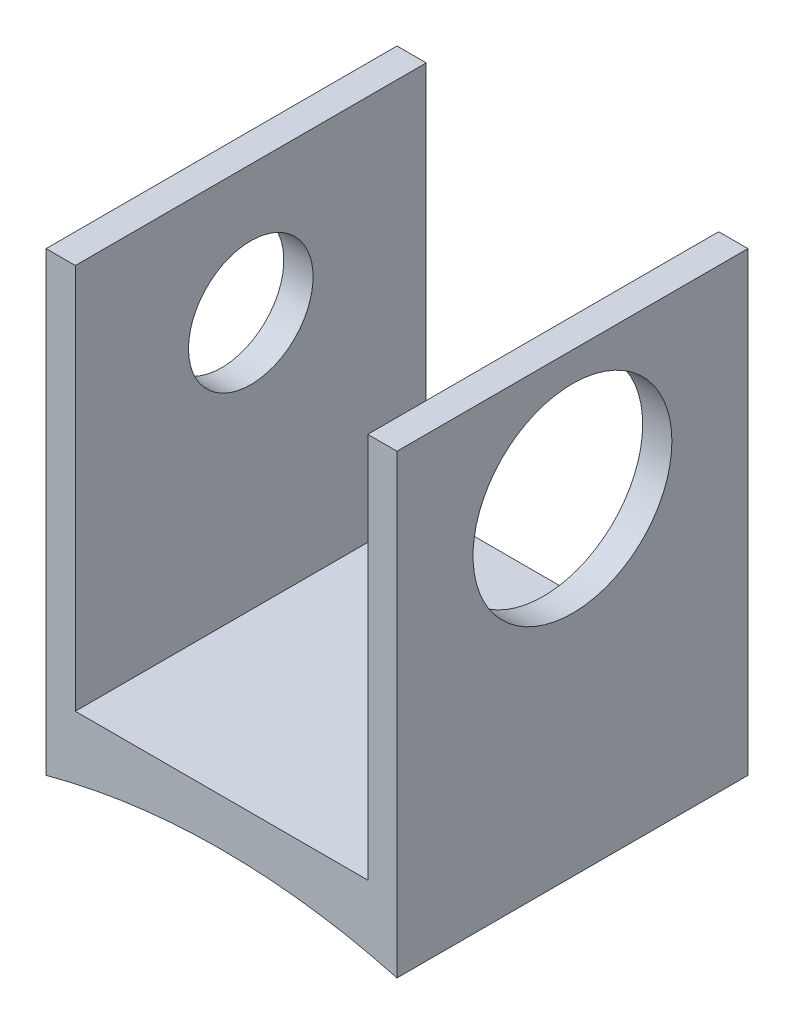
SolidWorks part; units mm, degrees
ref_plane "Front Plane" through (0, 0, 0) normal (0, 0, 1) x (1, 0, 0)
ref_plane "Top Plane" through (0, 0, 0) normal (0, 1, 0) x (1, 0, 0)
ref_plane "Right Plane" through (0, 0, 0) normal (1, 0, 0) x (0, 0, -1)
sketch "Sketch1" plane through (0, 0, 0) normal (0, 0, 1) x (1, 0, 0)
  line L0 (-3.3539, 7.6142) -> (-3.3539, -2.2918)
  line L1 (-3.3539, -2.2918) -> (4.2661, -2.2918)
  line L2 (4.2661, -2.2918) -> (4.2661, 7.6142)
  line L3 (3.6311, 7.6142) -> (3.6311, -0.7678)
  line L4 (3.6311, -0.7678) -> (-2.7189, -0.7678)
  line L5 (-2.7189, -0.7678) -> (-2.7189, 7.6142)
  line L6 (-2.7189, 7.6142) -> (-3.3539, 7.6142)
  line L7 (3.6311, 7.6142) -> (4.2661, 7.6142)
  dimension "D1" = 6.35
  dimension "D2" = 7.62
  dimension "D3" = 0.635
  dimension "D4" = 8.382
  dimension "D5" = 9.906
  dimension "D6" = 8.382
extrude "Boss-Extrude1" add sketch "Sketch1" along normal blind 7.62
sketch "Sketch2" plane through (-3.3539, 0, 0) normal (-1, 0, 0) x (0, 0, 1)
  line L0 (7.62, 7.6142) -> (0, 7.6142) construction
  line L1 (3.81, -2.2918) -> (3.81, 6.8522) construction
  point P0 (3.81, 4.8202)
  dimension "D1" = 2.794
hole_wizard "#6-32 Tapped Hole1" positions "Sketch3" profile "Sketch4" tap size "#6-32" standard "ANSI Inch" end condition up to next
sketch "Sketch3" plane through (-3.3539, 0, 0) normal (-1, 0, 0) x (0, 0, 1)
  point P0 (3.81, 4.8202)
sketch "Sketch4" plane through (-3.3539, 4.8202, 3.81) normal (0, 1, 0) x (0, 0, 1)
  line L0 (0, 0) -> (0, 0.635)
  line L1 (0, 0.635) -> (1.3525, 0.635)
  line L2 (1.3525, 0.635) -> (1.3525, 0)
  line L5 (1.3525, 0) -> (0, 0)
  line L11 (0, -6.35) -> (0, 107.95) construction
  dimension "Thread Major Dia." = 2.7051
  dimension "Thru Tap Drill Depth" = 0.635
sketch "Sketch5" plane through (4.2661, 0, 0) normal (1, 0, 0) x (0, 0, -1)
  point P0 (-3.81, 4.8202)
sketch "Sketch6" plane through (4.2661, 0, 0) normal (1, 0, 0) x (0, 0, -1)
  circle A0 centre (-3.81, 4.8202) radius 2.159
extrude "Cut-Extrude1" cut sketch "Sketch6" against normal up to next
sketch "Sketch12" plane through (-3.3539, 0, 0) normal (-1, 0, 0) x (0, 0, 1)
  line L0 (3.81, -2.2918) -> (3.81, 7.6142) construction
  line L1 (7.62, -2.2918) -> (0, -2.2918) construction
  line L2 (7.62, 7.6142) -> (0, 7.6142) construction
ref_plane "Plane1" through (0.508, 0, 0) normal (1, 0, 0) x (0, 0, -1)
sketch "Sketch14" plane through (0, 0, 0) normal (0, 0, -1) x (-1, 0, 0)
  line L0 (3.3539, -1.5298) -> (-4.2661, -1.5298) construction
  line L1 (3.3539, 7.6142) -> (3.3539, -2.2918) construction
  line L2 (-4.2661, -2.2918) -> (-4.2661, 7.6142) construction
  line L3 (3.3539, -2.2918) -> (-4.2661, -2.2918) construction
  dimension "D1" = 0.762
sketch "Sketch16" plane through (0, 0, 0) normal (0, 0, -1) x (-1, 0, 0)
  line L0 (-4.2661, -2.2918) -> (-0.4561, -16.2595) construction
  line L1 (-0.4561, -16.2595) -> (3.3539, -2.2918) construction
  line L2 (3.3539, -2.2918) -> (-4.2661, -2.2918)
  arc A0 (-4.2661, -2.2918) -> (3.3539, -2.2918) centre (-0.4561, -16.2595) cw
  dimension "D1" = 14.478
  dimension "D2" = 14.478
extrude "Cut-Extrude2" cut sketch "Sketch16" against normal through all
ref_plane "Plane2" through (0, 0, 3.81) normal (0, 0, -1) x (-1, 0, 0)
